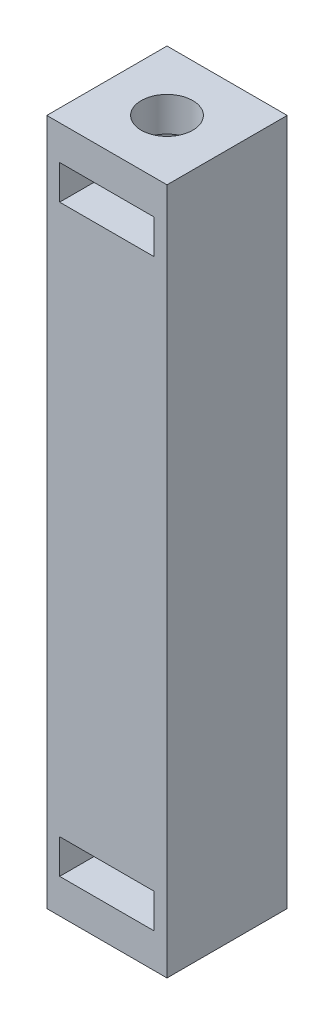
SolidWorks part; units mm, degrees
ref_plane "Front Plane" through (0, 0, 0) normal (0, 0, 1) x (1, 0, 0)
ref_plane "Top Plane" through (0, 0, 0) normal (0, 1, 0) x (1, 0, 0)
ref_plane "Right Plane" through (0, 0, 0) normal (1, 0, 0) x (0, 0, -1)
sketch "Sketch1" plane through (0, 0, 0) normal (0, 1, 0) x (1, 0, 0)
  line L1 (-3.5, 3.5) -> (3.5, 3.5)
  line L2 (-3.5, 3.5) -> (-3.5, -3.5)
  line L3 (-3.5, -3.5) -> (3.5, -3.5)
  line L4 (3.5, 3.5) -> (3.5, -3.5)
  line L5 (-3.5, 3.5) -> (3.5, -3.5) construction
  line L6 (-3.5, -3.5) -> (3.5, 3.5) construction
  point P0 (0, 0)
  point P6 (-3.5, 0)
  dimension "D1" = 7
  dimension "D2" = 7
  dimension "D3" = 7
extrude "Boss-Extrude1" add sketch "Sketch1" along normal blind 40
sketch "Sketch2" plane through (0, 40, 0) normal (0, 1, 0) x (1, 0, 0)
  circle A0 centre (0, 0) radius 1.5
extrude "Cut-Extrude1" cut sketch "Sketch2" against normal blind 41
sketch "Sketch3" plane through (0, 0, 3.5) normal (0, 0, 1) x (1, 0, 0)
  line L0 (0, 40) -> (0, 20) construction
  line L3 (-3.5, 20) -> (3.5, 20) construction
  line L4 (-3.5, 40) -> (-3.5, 0) construction
  line L5 (3.5, 40) -> (3.5, 0) construction
  line L14 (-3.5, 40) -> (3.5, 40) construction
  line L15 (-2.75, 2) -> (2.75, 2)
  line L16 (-2.75, 36) -> (2.75, 36)
  line L17 (-2.75, 36) -> (-2.75, 38)
  line L18 (-2.75, 38) -> (2.75, 38)
  line L19 (2.75, 36) -> (2.75, 38)
  line L20 (-2.75, 36) -> (2.75, 38) construction
  line L21 (-2.75, 38) -> (2.75, 36) construction
  line L22 (2.75, 4) -> (2.75, 2)
  line L23 (-2.75, 4) -> (2.75, 4)
  line L24 (-2.75, 4) -> (-2.75, 2)
  point P4 (0, 37)
  dimension "D1" = 2
  dimension "D2" = 5.5
  dimension "D3" = 2
extrude "Cut-Extrude2" cut sketch "Sketch3" against normal blind 41
